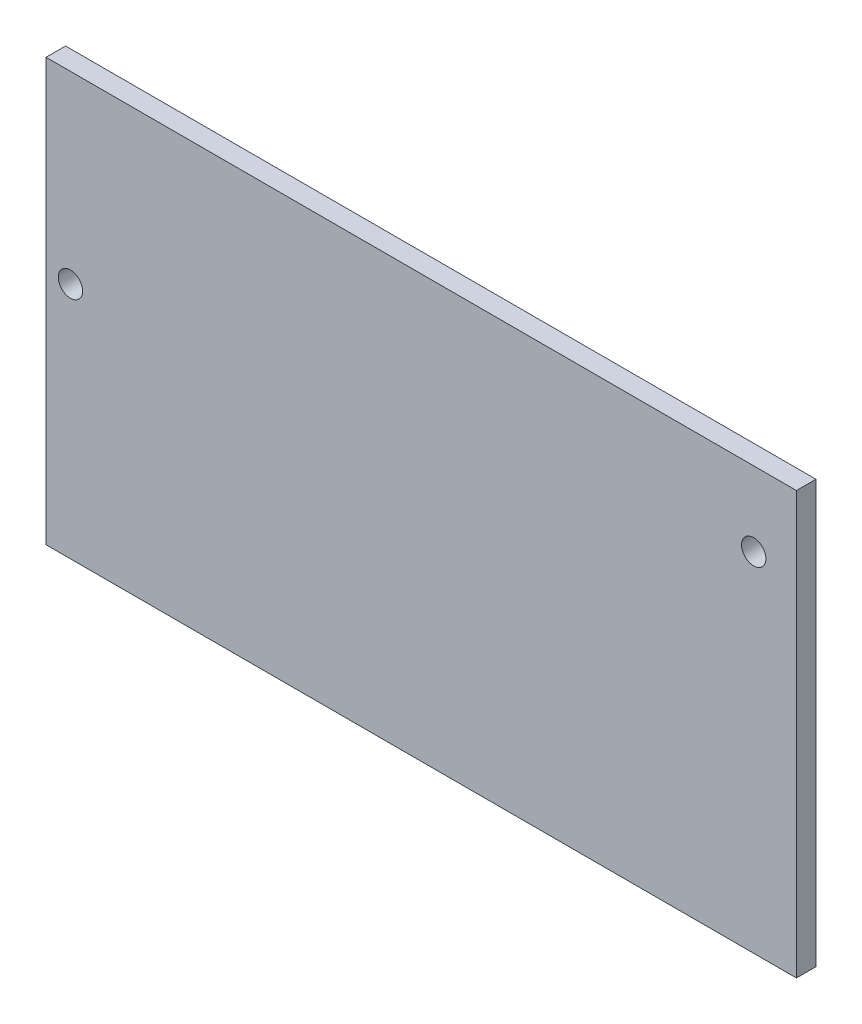
SolidWorks part; units mm, degrees
ref_plane "Front Plane" through (0, 0, 0) normal (0, 0, 1) x (1, 0, 0)
ref_plane "Top Plane" through (0, 0, 0) normal (0, 1, 0) x (1, 0, 0)
ref_plane "Right Plane" through (0, 0, 0) normal (1, 0, 0) x (0, 0, -1)
sketch "Sketch1" plane through (0, 0, 0) normal (0, 0, 1) x (1, 0, 0)
  line L1 (0, 0) -> (61.5, 0)
  line L2 (0, 0) -> (0, 34.6)
  line L3 (0, 34.6) -> (61.5, 34.6)
  line L4 (61.5, 0) -> (61.5, 34.6)
  circle A0 centre (2, 19.5) radius 1
  circle A1 centre (58, 28.5) radius 1
  dimension "D3" = 2
  dimension "D4" = 19.5
  dimension "D5" = 56
  dimension "D6" = 9
  dimension "D7" = 2
  dimension "D1" = 61.5
  dimension "D2" = 34.6
extrude "Boss-Extrude1" add sketch "Sketch1" along normal blind 1.6
